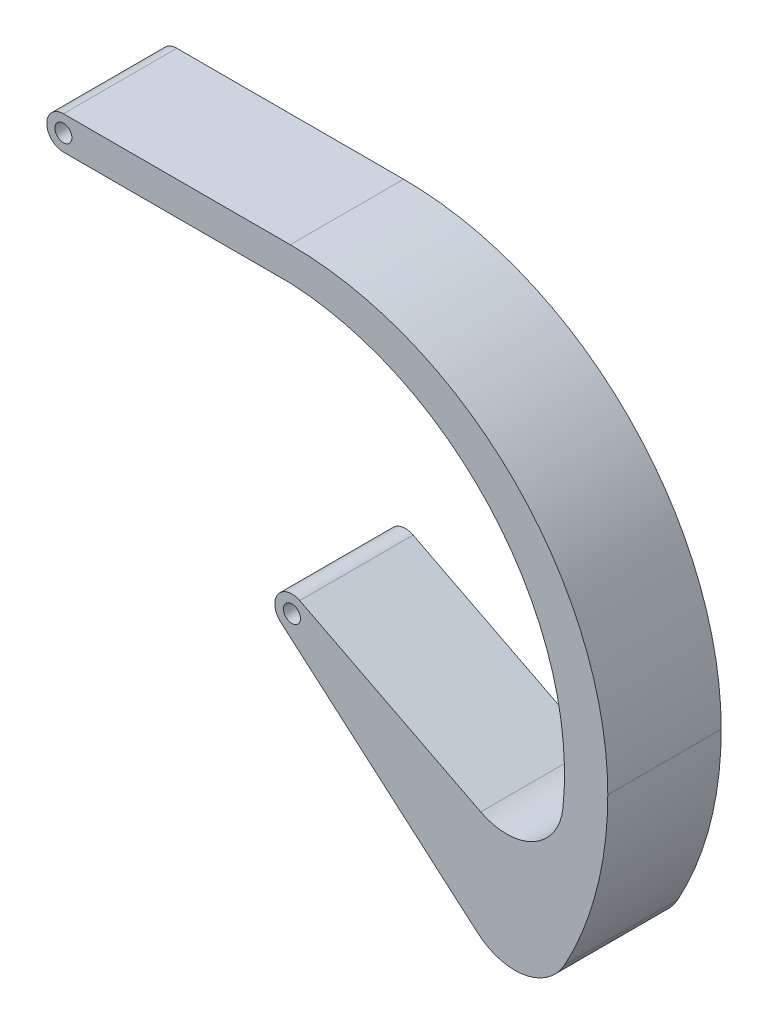
SolidWorks part; units mm, degrees
ref_plane "Front Plane" through (0, 0, 0) normal (0, 0, 1) x (1, 0, 0)
ref_plane "Top Plane" through (0, 0, 0) normal (0, 1, 0) x (1, 0, 0)
ref_plane "Right Plane" through (0, 0, 0) normal (1, 0, 0) x (0, 0, -1)
sketch "Sketch1" plane through (0, 0, 0) normal (0, 0, 1) x (1, 0, 0)
  line L0 (-1.5172, 0.343) -> (2.4828, 0.343)
  line L1 (-1.5172, -0.2427) -> (2.4828, -0.2427)
  line L7 (2.3151, -5.5058) -> (6.6315, -9.2444)
  line L9 (2.6505, -5.0083) -> (6.9559, -7.2095)
  arc A0 (-1.5172, 0.343) -> (-1.5172, -0.2427) centre (-1.5172, 0.0501) ccw
  arc A1 (2.4828, 0.343) -> (8.0828, -5.257) centre (2.4828, -5.257) cw
  arc A2 (8.0828, -5.257) -> (6.6315, -9.2444) centre (1.8795, -5.257) cw
  arc A3 (2.3151, -5.5058) -> (2.6505, -5.0083) centre (2.513, -5.2773) cw
  arc A4 (2.4828, -0.2427) -> (6.9559, -7.2095) centre (2.2352, -5.3211) cw
extrude "Boss-Extrude1" add sketch "Sketch1" along normal blind 2
sketch "Sketch2" plane through (0, 0, 0) normal (0, 0, -1) x (-1, 0, 0)
  circle A0 centre (-2.513, -5.2773) radius 0.15
  dimension "D1" = 0.3
extrude "Cut-Extrude1" cut sketch "Sketch2" against normal through all
sketch "Sketch3" plane through (0, 0, 0) normal (0, 0, -1) x (-1, 0, 0)
  circle A0 centre (1.5172, 0.0501) radius 0.15
  dimension "D1" = 0.3
extrude "Cut-Extrude4" cut sketch "Sketch3" against normal through all
fillet "Fillet2" radius 1 1 edges at (6.6315, -9.2444, 1)
fillet "Fillet3" radius 1 1 edges at (6.9559, -7.2095, 1)
scale "Scale2" scale about centroid uniform scaling yes scale factor 10
